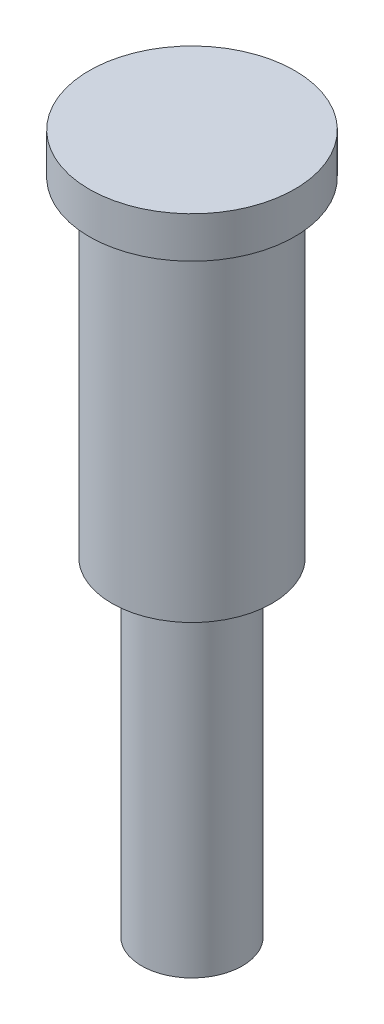
SolidWorks part; units mm, degrees
ref_plane "Front Plane" through (0, 0, 0) normal (0, 0, 1) x (1, 0, 0)
ref_plane "Top Plane" through (0, 0, 0) normal (0, 1, 0) x (1, 0, 0)
ref_plane "Right Plane" through (0, 0, 0) normal (1, 0, 0) x (0, 0, -1)
sketch "Sketch1" plane through (0, 0, 0) normal (0, 1, 0) x (1, 0, 0)
  circle A0 centre (0, 0) radius 5
  circle A1 centre (0, 0) radius 6
  dimension "D1" = 10
  dimension "D2" = 1
extrude "Boss-Extrude1" add sketch "Sketch1" along normal blind 2 contours A0
sketch "Sketch4" plane through (0, 0, 0) normal (0, -1, 0) x (-1, 0, 0)
  circle A1 centre (0, 0) radius 3.9
  dimension "D2" = 7.8
extrude "Boss-Extrude2" add sketch "Sketch4" along normal blind 16
ref_plane "Plane1" through (0, -13.5, 0) normal (0, -1, 0) x (-1, 0, 0)
sketch "Sketch6" plane through (0, -16, 0) normal (0, -1, 0) x (-1, 0, 0)
  circle A0 centre (0, 0) radius 2.45
  circle A1 centre (0, 0) radius 1.6
  dimension "D1" = 4.9
  dimension "D2" = 3.2
extrude "Boss-Extrude3" add sketch "Sketch6" along normal blind 16
